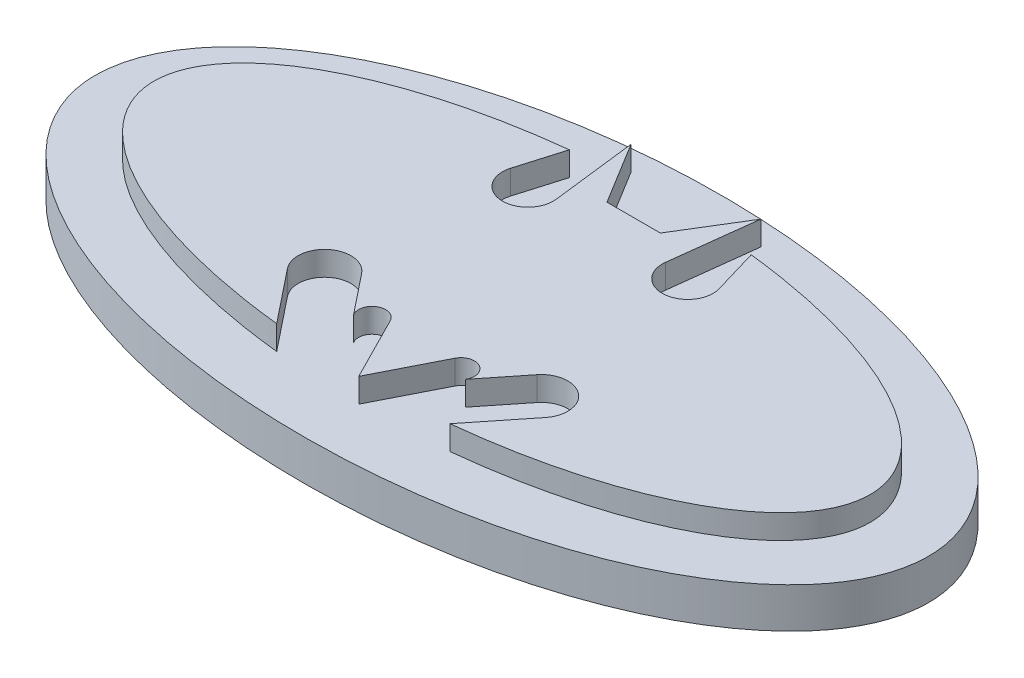
SolidWorks part; units mm, degrees
ref_plane "Front Plane" through (0, 0, 0) normal (0, 0, 1) x (1, 0, 0)
ref_plane "Top Plane" through (0, 0, 0) normal (0, 1, 0) x (1, 0, 0)
ref_plane "Right Plane" through (0, 0, 0) normal (1, 0, 0) x (0, 0, -1)
sketch "Sketch1" plane through (0, 0, 0) normal (0, 1, 0) x (1, 0, 0)
  line L0 (0, 41.6471) -> (0, -48.8576) construction
  line L1 (-59.329, 0) -> (-44.516, 0) construction
  line L2 (-3.3217, 15.1221) -> (3.3217, 15.1221)
  line L3 (3.3217, 15.1221) -> (8.0649, 22.861)
  line L4 (8.0649, 22.861) -> (6.7906, 12.2827)
  line L5 (12.9652, 12.8001) -> (11.3044, 18.4253)
  line L6 (0, -19.0497) -> (4.0256, -11.1162)
  line L7 (6.9513, -12.7472) -> (10.9115, -7.7822)
  line L8 (16.0424, -11.8746) -> (10.7709, -18.4837)
  line L9 (-59.2162, 0) -> (59.2162, 0) construction
  line L10 (-16.0424, -11.8746) -> (-10.7709, -18.4837)
  line L11 (-6.9513, -12.7472) -> (-10.9115, -7.7822)
  line L12 (0, -19.0497) -> (-4.0256, -11.1162)
  line L13 (-12.9652, 12.8001) -> (-11.3044, 18.4253)
  line L14 (-8.0649, 22.861) -> (-6.7906, 12.2827)
  line L15 (-3.3217, 15.1221) -> (-8.0649, 22.861)
  arc A0 (6.7906, 12.2827) -> (12.9652, 12.8001) centre (9.9313, 11.9044) ccw
  arc A1 (4.0256, -11.1162) -> (6.9513, -12.7472) centre (5.5203, -11.8746) cw
  arc A2 (10.9115, -7.7822) -> (16.0424, -11.8746) centre (13.4769, -9.8284) cw
  arc A3 (-10.9115, -7.7822) -> (-16.0424, -11.8746) centre (-13.4769, -9.8284) ccw
  arc A4 (-4.0256, -11.1162) -> (-6.9513, -12.7472) centre (-5.5203, -11.8746) ccw
  arc A5 (-6.7906, 12.2827) -> (-12.9652, 12.8001) centre (-9.9313, 11.9044) cw
  ellipse E0 centre (0, 0) end of major axis (-44.516, 0) minor radius 19.0497 (10.7709, -18.4837) -> (11.3044, 18.4253) ccw
  ellipse E1 centre (0, 0) end of major axis (44.516, 0) minor radius 19.0497 (-10.7709, -18.4837) -> (-11.3044, 18.4253) cw
  point P18 (3.3217, 15.1221)
  point P25 (44.516, 0)
  point P26 (0, 19.0497)
  point P27 (6.9513, 12.8001)
  point P28 (8.0649, 22.861)
  point P49 (0, 15.1221)
extrude "Boss-Extrude1" add sketch "Sketch1" along normal blind 3
sketch "Sketch3" plane through (0, 0, 0) normal (0, -1, 0) x (1, 0, 0)
  ellipse E0 centre (0, 0) end of major axis (-51.7874, 0) minor radius 25.9799
extrude "Boss-Extrude2" add sketch "Sketch3" along normal blind 5
